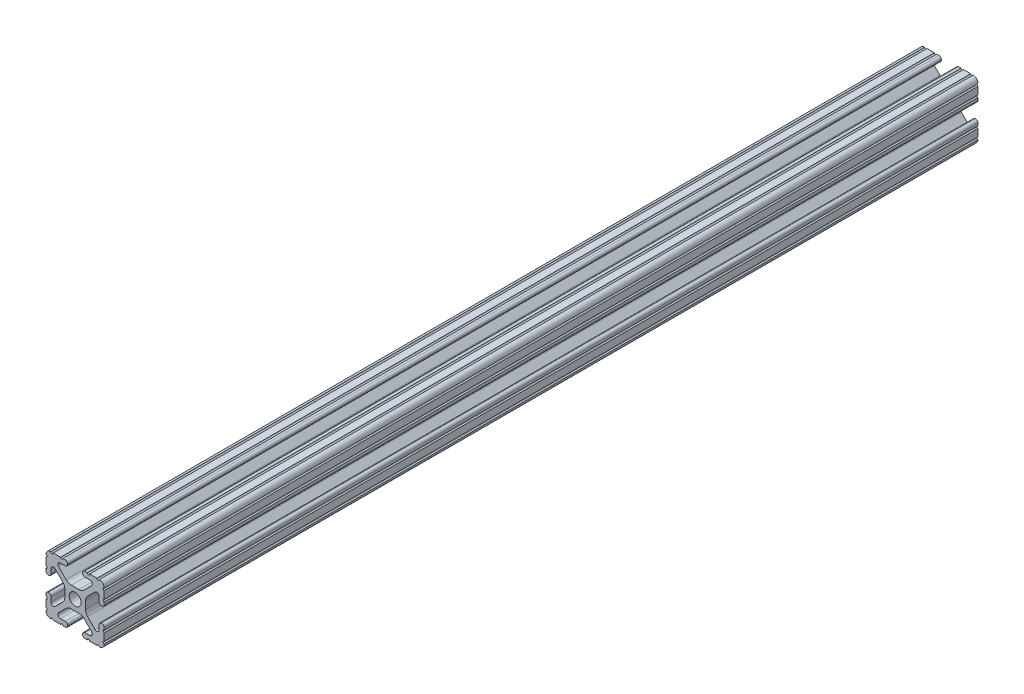
SolidWorks part; units mm, degrees
ref_plane "Front Plane" through (0, 0, 0) normal (0, 0, 1) x (1, 0, 0)
ref_plane "Top Plane" through (0, 0, 0) normal (0, 1, 0) x (1, 0, 0)
ref_plane "Right Plane" through (0, 0, 0) normal (1, 0, 0) x (0, 0, -1)
sketch "Sketch1" plane through (0, 0, 0) normal (0, 0, 1) x (1, 0, 0)
  line L88 (-7.1797, -8.6452) -> (-3.9523, -5.4237)
  line L89 (-1.7093, -4.4958) -> (1.7093, -4.4958)
  line L90 (3.9523, -5.4237) -> (7.1797, -8.6452)
  line L91 (6.4164, -10.4902) -> (4.2875, -10.4902)
  line L92 (3.2385, -11.5392) -> (3.2385, -11.651)
  line L93 (4.2875, -12.7) -> (5.3171, -12.7)
  line L94 (6.3331, -12.7) -> (9.5504, -12.7)
  line L95 (12.7, -9.5504) -> (12.7, -6.3331)
  line L96 (12.7, -5.3171) -> (12.7, -4.2875)
  line L97 (11.651, -3.2385) -> (11.5392, -3.2385)
  line L98 (10.4902, -4.2875) -> (10.4902, -6.4021)
  line L99 (8.7371, -7.1294) -> (5.441, -3.8408)
  line L100 (4.5085, -1.5932) -> (4.5085, 1.5932)
  line L101 (5.441, 3.8408) -> (8.7371, 7.1294)
  line L102 (10.4902, 6.4021) -> (10.4902, 4.2875)
  line L103 (11.5392, 3.2385) -> (11.651, 3.2385)
  line L104 (12.7, 4.2875) -> (12.7, 5.3171)
  line L105 (12.7, 6.3331) -> (12.7, 9.5504)
  line L106 (9.5504, 12.7) -> (6.3331, 12.7)
  line L107 (5.3171, 12.7) -> (4.2875, 12.7)
  line L108 (3.2385, 11.651) -> (3.2385, 11.5392)
  line L109 (4.2875, 10.4902) -> (6.4768, 10.4902)
  line L110 (7.207, 8.7244) -> (3.8983, 5.4232)
  line L111 (1.6558, 4.4958) -> (-1.6558, 4.4958)
  line L112 (-3.8983, 5.4232) -> (-7.207, 8.7244)
  line L113 (-6.4768, 10.4902) -> (-4.2875, 10.4902)
  line L114 (-3.2385, 11.5392) -> (-3.2385, 11.651)
  line L115 (-4.2875, 12.7) -> (-5.3171, 12.7)
  line L116 (-6.3331, 12.7) -> (-9.5504, 12.7)
  line L117 (-12.7, 9.5504) -> (-12.7, 6.3331)
  line L118 (-12.7, 5.3171) -> (-12.7, 4.2875)
  line L119 (-11.651, 3.2385) -> (-11.5392, 3.2385)
  line L120 (-10.4902, 4.2875) -> (-10.4902, 6.4021)
  line L121 (-8.7371, 7.1294) -> (-5.441, 3.8408)
  line L122 (-4.5085, 1.5932) -> (-4.5085, -1.5932)
  line L123 (-5.441, -3.8408) -> (-8.7371, -7.1294)
  line L124 (-10.4902, -6.4021) -> (-10.4902, -4.2875)
  line L125 (-11.5392, -3.2385) -> (-11.651, -3.2385)
  line L126 (-12.7, -4.2875) -> (-12.7, -5.3171)
  line L127 (-12.7, -6.3331) -> (-12.7, -9.5504)
  line L128 (-9.5504, -12.7) -> (-6.3331, -12.7)
  line L129 (-5.3171, -12.7) -> (-4.2875, -12.7)
  line L130 (-3.2385, -11.651) -> (-3.2385, -11.5392)
  line L131 (-4.2875, -10.4902) -> (-6.4164, -10.4902)
  circle A1 centre (0, 0) radius 2.6035
  arc A104 (-7.1797, -8.6452) -> (-6.4164, -10.4902) centre (-6.4164, -9.4098) ccw
  arc A105 (-1.7093, -4.4958) -> (-3.9523, -5.4237) centre (-1.7093, -7.6708) ccw
  arc A106 (3.9523, -5.4237) -> (1.7093, -4.4958) centre (1.7093, -7.6708) ccw
  arc A107 (6.4164, -10.4902) -> (7.1797, -8.6452) centre (6.4164, -9.4098) ccw
  arc A108 (4.2875, -10.4902) -> (3.2385, -11.5392) centre (4.2875, -11.5392) ccw
  arc A109 (3.2385, -11.651) -> (4.2875, -12.7) centre (4.2875, -11.651) ccw
  arc A110 (6.3331, -12.7) -> (5.3171, -12.7) centre (5.8251, -12.7) ccw
  arc A111 (10.5664, -12.6998) -> (9.5504, -12.7) centre (10.0584, -12.7) ccw
  arc A112 (10.5664, -12.6998) -> (12.6998, -10.5664) centre (10.5918, -10.5918) ccw
  arc A113 (12.7, -9.5504) -> (12.6998, -10.5664) centre (12.7, -10.0584) ccw
  arc A114 (12.7, -5.3171) -> (12.7, -6.3331) centre (12.7, -5.8251) ccw
  arc A115 (12.7, -4.2875) -> (11.651, -3.2385) centre (11.651, -4.2875) ccw
  arc A116 (11.5392, -3.2385) -> (10.4902, -4.2875) centre (11.5392, -4.2875) ccw
  arc A117 (8.7371, -7.1294) -> (10.4902, -6.4021) centre (9.4628, -6.4021) ccw
  arc A118 (4.5085, -1.5932) -> (5.441, -3.8408) centre (7.6835, -1.5932) ccw
  arc A119 (5.441, 3.8408) -> (4.5085, 1.5932) centre (7.6835, 1.5932) ccw
  arc A120 (10.4902, 6.4021) -> (8.7371, 7.1294) centre (9.4628, 6.4021) ccw
  arc A121 (10.4902, 4.2875) -> (11.5392, 3.2385) centre (11.5392, 4.2875) ccw
  arc A122 (11.651, 3.2385) -> (12.7, 4.2875) centre (11.651, 4.2875) ccw
  arc A123 (12.7, 6.3331) -> (12.7, 5.3171) centre (12.7, 5.8251) ccw
  arc A124 (12.6998, 10.5664) -> (12.7, 9.5504) centre (12.7, 10.0584) ccw
  arc A125 (12.6998, 10.5664) -> (10.5664, 12.6998) centre (10.5918, 10.5918) ccw
  arc A126 (9.5504, 12.7) -> (10.5664, 12.6998) centre (10.0584, 12.7) ccw
  arc A127 (5.3171, 12.7) -> (6.3331, 12.7) centre (5.8251, 12.7) ccw
  arc A128 (4.2875, 12.7) -> (3.2385, 11.651) centre (4.2875, 11.651) ccw
  arc A129 (3.2385, 11.5392) -> (4.2875, 10.4902) centre (4.2875, 11.5392) ccw
  arc A130 (7.207, 8.7244) -> (6.4768, 10.4902) centre (6.4768, 9.4563) ccw
  arc A131 (1.6558, 4.4958) -> (3.8983, 5.4232) centre (1.6558, 7.6708) ccw
  arc A132 (-3.8983, 5.4232) -> (-1.6558, 4.4958) centre (-1.6558, 7.6708) ccw
  arc A133 (-6.4768, 10.4902) -> (-7.207, 8.7244) centre (-6.4768, 9.4563) ccw
  arc A134 (-4.2875, 10.4902) -> (-3.2385, 11.5392) centre (-4.2875, 11.5392) ccw
  arc A135 (-3.2385, 11.651) -> (-4.2875, 12.7) centre (-4.2875, 11.651) ccw
  arc A136 (-6.3331, 12.7) -> (-5.3171, 12.7) centre (-5.8251, 12.7) ccw
  arc A137 (-10.5664, 12.6998) -> (-9.5504, 12.7) centre (-10.0584, 12.7) ccw
  arc A138 (-10.5664, 12.6998) -> (-12.6998, 10.5664) centre (-10.5918, 10.5918) ccw
  arc A139 (-12.7, 9.5504) -> (-12.6998, 10.5664) centre (-12.7, 10.0584) ccw
  arc A140 (-12.7, 5.3171) -> (-12.7, 6.3331) centre (-12.7, 5.8251) ccw
  arc A141 (-12.7, 4.2875) -> (-11.651, 3.2385) centre (-11.651, 4.2875) ccw
  arc A142 (-11.5392, 3.2385) -> (-10.4902, 4.2875) centre (-11.5392, 4.2875) ccw
  arc A143 (-8.7371, 7.1294) -> (-10.4902, 6.4021) centre (-9.4628, 6.4021) ccw
  arc A144 (-4.5085, 1.5932) -> (-5.441, 3.8408) centre (-7.6835, 1.5932) ccw
  arc A145 (-5.441, -3.8408) -> (-4.5085, -1.5932) centre (-7.6835, -1.5932) ccw
  arc A146 (-10.4902, -6.4021) -> (-8.7371, -7.1294) centre (-9.4628, -6.4021) ccw
  arc A147 (-10.4902, -4.2875) -> (-11.5392, -3.2385) centre (-11.5392, -4.2875) ccw
  arc A148 (-11.651, -3.2385) -> (-12.7, -4.2875) centre (-11.651, -4.2875) ccw
  arc A149 (-12.7, -6.3331) -> (-12.7, -5.3171) centre (-12.7, -5.8251) ccw
  arc A150 (-12.6998, -10.5664) -> (-12.7, -9.5504) centre (-12.7, -10.0584) ccw
  arc A151 (-12.6998, -10.5664) -> (-10.5664, -12.6998) centre (-10.5918, -10.5918) ccw
  arc A152 (-9.5504, -12.7) -> (-10.5664, -12.6998) centre (-10.0584, -12.7) ccw
  arc A153 (-5.3171, -12.7) -> (-6.3331, -12.7) centre (-5.8251, -12.7) ccw
  arc A154 (-4.2875, -12.7) -> (-3.2385, -11.651) centre (-4.2875, -11.651) ccw
  arc A155 (-3.2385, -11.5392) -> (-4.2875, -10.4902) centre (-4.2875, -11.5392) ccw
extrude "Boss-Extrude1" add sketch "Sketch1" along normal mid plane 381
